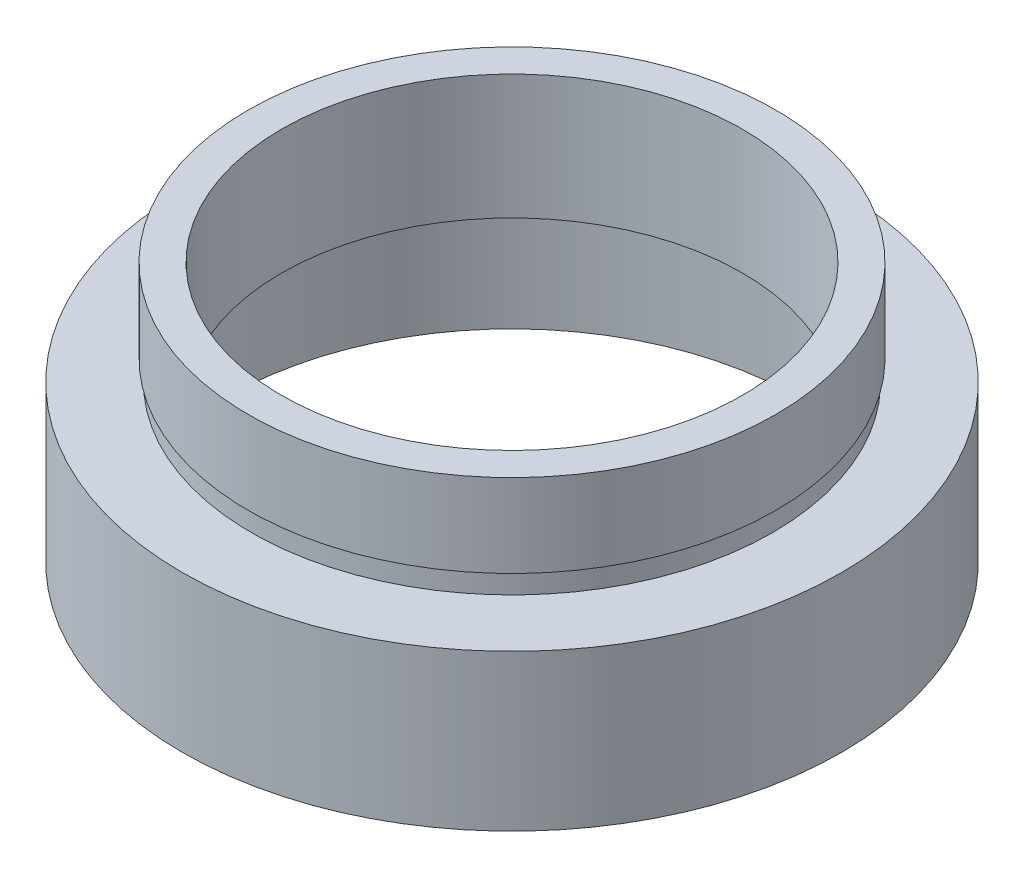
SolidWorks part; units mm, degrees
ref_plane "前视基准面" through (0, 0, 0) normal (0, 0, 1) x (1, 0, 0)
ref_plane "上视基准面" through (0, 0, 0) normal (0, 1, 0) x (1, 0, 0)
ref_plane "右视基准面" through (0, 0, 0) normal (1, 0, 0) x (0, 0, -1)
sketch "草图1" plane through (0, 0, 0) normal (0, 0, 1) x (1, 0, 0)
  line L0 (0, 16.886) -> (0, -24.4878) construction
  line L1 (13.75, 0) -> (13.75, 5.5)
  line L2 (11.1, 6.5) -> (14.35, 6.5)
  line L3 (11.1, 6.5) -> (11.1, 12.5)
  line L4 (11.1, 12.5) -> (12.7, 12.5)
  line L5 (12.7, 12.5) -> (12.7, 8.5)
  line L6 (12.7, 8.5) -> (12.55, 8.5)
  line L7 (12.55, 8.5) -> (12.55, 7.5)
  line L8 (12.55, 7.5) -> (15.875, 7.5)
  line L9 (15.875, 7.5) -> (15.875, 0)
  line L10 (15.875, 0) -> (13.75, 0)
  line L11 (13.75, 5.5) -> (14.35, 5.5)
  line L12 (14.35, 5.5) -> (14.35, 6.5)
  line L13 (0, 0) -> (3.4668, 0) construction
  point P4 (14.8125, 0)
  dimension "D1" = 11.1
  dimension "D2" = 12.7
  dimension "D3" = 12.55
  dimension "D4" = 13.75
  dimension "D5" = 14.35
  dimension "D6" = 15.875
  dimension "D7" = 12.5
  dimension "D8" = 7.5
  dimension "D9" = 1
  dimension "D10" = 5.5
  dimension "D11" = 1
revolve "旋转1" add sketch "草图1" angle 360 about L0
cosmetic thread "装饰螺纹线1" parameters "D2"=24.4
cosmetic thread "装饰螺纹线2" parameters "D2"=23.2
cosmetic thread "装饰螺纹线3" parameters "D2"=28.5
